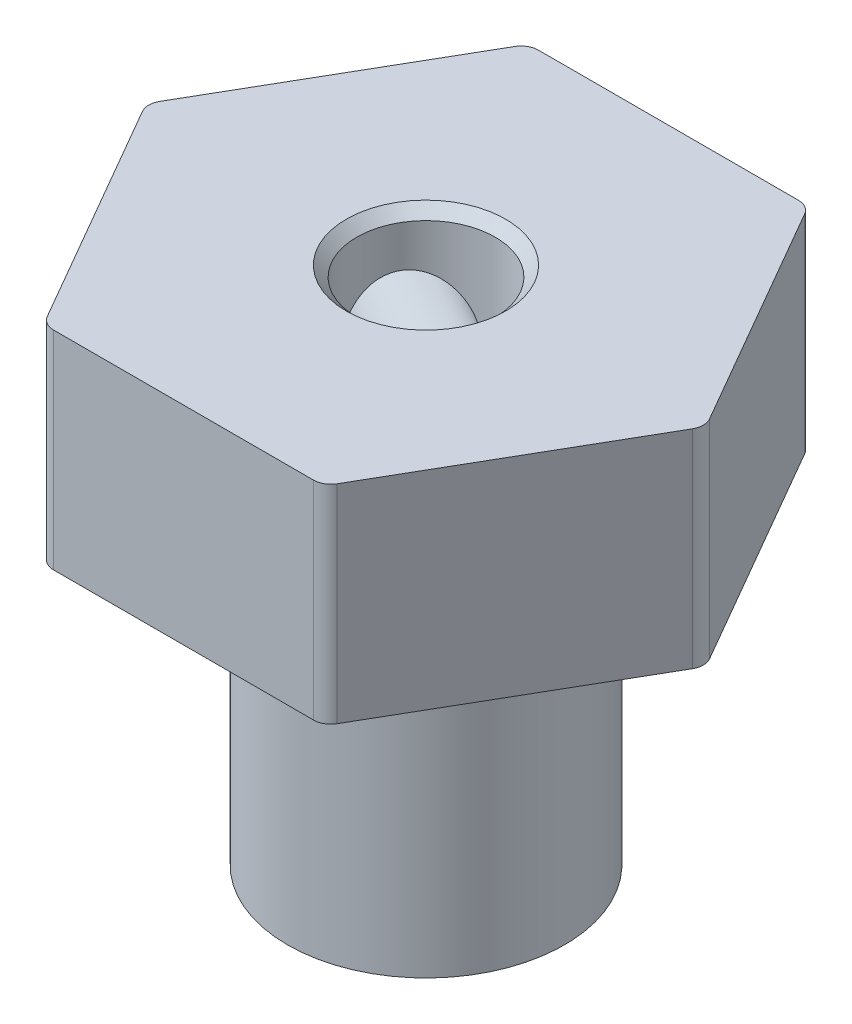
SolidWorks part; units mm, degrees
material "1060 Alloy"
ref_plane "Front Plane" through (0, 0, 0) normal (0, 0, 1) x (1, 0, 0)
ref_plane "Top Plane" through (0, 0, 0) normal (0, 1, 0) x (1, 0, 0)
ref_plane "Right Plane" through (0, 0, 0) normal (1, 0, 0) x (0, 0, -1)
sketch "Sketch1" plane through (0, 0, 0) normal (0, 1, 0) x (1, 0, 0)
  line L1 (8.0829, 0) -> (4.0415, 7)
  line L2 (4.0415, 7) -> (-4.0415, 7)
  line L3 (-4.0415, 7) -> (-8.0829, 0)
  line L4 (-8.0829, 0) -> (-4.0415, -7)
  line L5 (-4.0415, -7) -> (4.0415, -7)
  line L6 (4.0415, -7) -> (8.0829, 0)
  circle A0 centre (0, 0) radius 7 construction
  dimension "D1" = 14
extrude "Boss-Extrude1" add sketch "Sketch1" along normal blind 6
fillet "Fillet1" radius 0.5 6 edges at (-4.0415, 3, 7) (-8.0829, 3, 0) (-4.0415, 3, -7) (4.0415, 3, -7) (8.0829, 3, 0) (4.0415, 3, 7)
sketch "Sketch2" plane through (0, 0, 0) normal (0, -1, 0) x (1, 0, 0)
  circle A0 centre (0, 0) radius 4
  dimension "D1" = 8
extrude "Boss-Extrude2" add sketch "Sketch2" along normal blind 9
sketch "Sketch4" plane through (0, 6, 0) normal (0, 1, 0) x (1, 0, 0)
  circle A0 centre (0, 0) radius 2
  dimension "D1" = 4
extrude "Cut-Extrude1" cut sketch "Sketch4" against normal through all
chamfer "Chamfer1" distance 0.3 angle 45 1 edges at (0, 6, 2)
sketch "Sketch5" plane through (-6.0622, 0, -3.5) normal (-0.866, 0, -0.5) x (-0.5, 0, 0.866)
  line L0 (-3.7528, 3) -> (3.7528, 3) construction
  line L1 (-3.7528, 6) -> (-3.7528, 0) construction
  line L2 (3.7528, 0) -> (3.7528, 6) construction
  circle A0 centre (0, 3) radius 1.5
  dimension "D1" = 3
extrude "Cut-Extrude2" cut sketch "Sketch5" against normal blind 8
